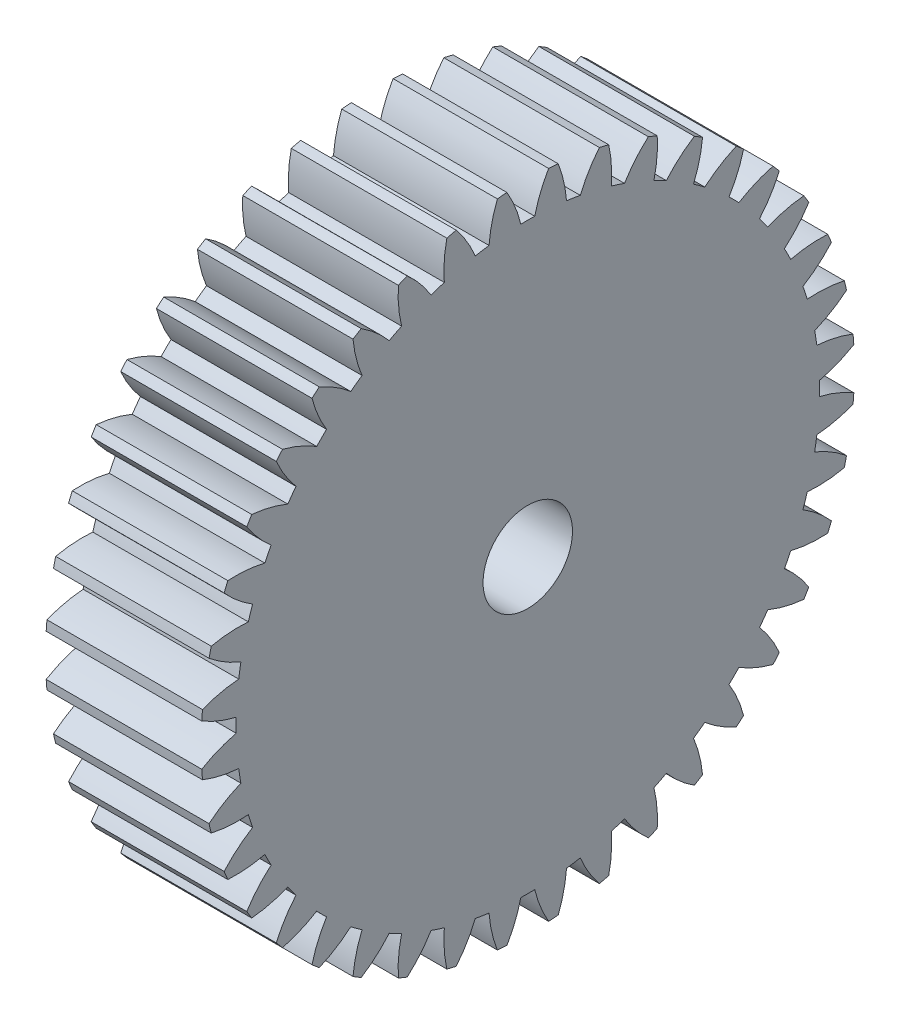
SolidWorks part; units mm, degrees
ref_plane "Front Plane" through (0, 0, 0) normal (0, 0, 1) x (1, 0, 0)
ref_plane "Top Plane" through (0, 0, 0) normal (0, 1, 0) x (1, 0, 0)
ref_plane "Right Plane" through (0, 0, 0) normal (1, 0, 0) x (0, 0, -1)
ref_plane "Plane1" through (-1.595, 0, 0) normal (1, 0, 0) x (0, 0, -1)
sketch "Sketch1" plane through (-1.595, 0, 0) normal (1, 0, 0) x (0, 0, -1)
  circle A0 centre (-8.0381, 6.9342) radius 0.4
  arc A1 (-16.421, 7.4699) -> (-15.535, 7.1132) centre (-14.7963, 10.2268) ccw
  arc A2 (-15.535, 7.1132) -> (-15.535, 6.7552) centre (-8.0381, 6.9342) ccw
  arc A3 (-15.535, 6.7552) -> (-16.421, 6.3985) centre (-14.7963, 3.6417) ccw
  arc A4 (-16.421, 6.3985) -> (-16.4016, 6.152) centre (-8.0381, 6.9342) ccw
  arc A5 (-16.4016, 6.152) -> (-15.4707, 5.9382) centre (-15.2282, 9.129) ccw
  arc A6 (-15.4707, 5.9382) -> (-15.4147, 5.5847) centre (-8.0381, 6.9342) ccw
  arc A7 (-15.4147, 5.5847) -> (-16.234, 5.0937) centre (-14.198, 2.625) ccw
  arc A8 (-16.234, 5.0937) -> (-16.1763, 4.8533) centre (-8.0381, 6.9342) ccw
  arc A9 (-16.1763, 4.8533) -> (-15.2234, 4.7878) centre (-15.483, 7.9773) ccw
  arc A10 (-15.2234, 4.7878) -> (-15.1128, 4.4473) centre (-8.0381, 6.9342) ccw
  arc A11 (-15.1128, 4.4473) -> (-15.8452, 3.8343) centre (-13.4481, 1.7144) ccw
  arc A12 (-15.8452, 3.8343) -> (-15.7506, 3.6058) centre (-8.0381, 6.9342) ccw
  arc A13 (-15.7506, 3.6058) -> (-14.7992, 3.6902) centre (-15.5545, 6.7998) ccw
  arc A14 (-14.7992, 3.6902) -> (-14.6366, 3.3712) centre (-8.0381, 6.9342) ccw
  arc A15 (-14.6366, 3.3712) -> (-15.2641, 2.6511) centre (-12.5649, 0.9324) ccw
  arc A16 (-15.2641, 2.6511) -> (-15.1349, 2.4403) centre (-8.0381, 6.9342) ccw
  arc A17 (-15.1349, 2.4403) -> (-14.2084, 2.6725) centre (-15.4409, 5.6256) ccw
  arc A18 (-14.2084, 2.6725) -> (-13.998, 2.3829) centre (-8.0381, 6.9342) ccw
  arc A19 (-13.998, 2.3829) -> (-14.5052, 1.5735) centre (-11.5703, 0.2981) ccw
  arc A20 (-14.5052, 1.5735) -> (-14.3446, 1.3854) centre (-8.0381, 6.9342) ccw
  arc A21 (-14.3446, 1.3854) -> (-13.4658, 1.7597) centre (-15.1451, 4.4837) ccw
  arc A22 (-13.4658, 1.7597) -> (-13.2127, 1.5066) centre (-8.0381, 6.9342) ccw
  arc A23 (-13.2127, 1.5066) -> (-13.5869, 0.6278) centre (-10.4887, -0.1727) ccw
  arc A24 (-13.5869, 0.6278) -> (-13.3989, 0.4672) centre (-8.0381, 6.9342) ccw
  arc A25 (-13.3989, 0.4672) -> (-12.5895, 0.9743) centre (-14.6742, 3.4021) ccw
  arc A26 (-12.5895, 0.9743) -> (-12.2999, 0.7639) centre (-8.0381, 6.9342) ccw
  arc A27 (-12.2999, 0.7639) -> (-12.5321, -0.1626) centre (-9.3467, -0.4686) ccw
  arc A28 (-12.5321, -0.1626) -> (-12.3212, -0.2918) centre (-8.0381, 6.9342) ccw
  arc A29 (-12.3212, -0.2918) -> (-11.6011, 0.3357) centre (-14.04, 2.4075) ccw
  arc A30 (-11.6011, 0.3357) -> (-11.2822, 0.1732) centre (-8.0381, 6.9342) ccw
  arc A31 (-11.2822, 0.1732) -> (-11.3666, -0.7782) centre (-8.1726, -0.5821) ccw
  arc A32 (-11.3666, -0.7782) -> (-11.1381, -0.8728) centre (-8.0381, 6.9342) ccw
  arc A33 (-11.1381, -0.8728) -> (-10.525, -0.1404) centre (-13.2579, 1.5243) ccw
  arc A34 (-10.525, -0.1404) -> (-10.1846, -0.251) centre (-8.0381, 6.9342) ccw
  arc A35 (-10.1846, -0.251) -> (-10.1191, -1.2039) centre (-6.9951, -0.5106) ccw
  arc A36 (-10.1191, -1.2039) -> (-9.8786, -1.2617) centre (-8.0381, 6.9342) ccw
  arc A37 (-9.8786, -1.2617) -> (-9.3877, -0.4423) centre (-12.3474, 0.7744) ccw
  arc A38 (-9.3877, -0.4423) -> (-9.0341, -0.4984) centre (-8.0381, 6.9342) ccw
  arc A39 (-9.0341, -0.4984) -> (-8.8204, -1.4293) centre (-5.8433, -0.2558) ccw
  arc A40 (-8.8204, -1.4293) -> (-8.5739, -1.4487) centre (-8.0381, 6.9342) ccw
  arc A41 (-8.5739, -1.4487) -> (-8.2171, -0.5626) centre (-11.3307, 0.1761) ccw
  arc A42 (-8.2171, -0.5626) -> (-7.8591, -0.5626) centre (-8.0381, 6.9342) ccw
  arc A43 (-7.8591, -0.5626) -> (-7.5024, -1.4487) centre (-4.7456, 0.1761) ccw
  arc A44 (-7.5024, -1.4487) -> (-7.2559, -1.4293) centre (-8.0381, 6.9342) ccw
  arc A45 (-7.2559, -1.4293) -> (-7.0422, -0.4984) centre (-10.233, -0.2558) ccw
  arc A46 (-7.0422, -0.4984) -> (-6.6886, -0.4423) centre (-8.0381, 6.9342) ccw
  arc A47 (-6.6886, -0.4423) -> (-6.1976, -1.2617) centre (-3.7289, 0.7744) ccw
  arc A48 (-6.1976, -1.2617) -> (-5.9572, -1.2039) centre (-8.0381, 6.9342) ccw
  arc A49 (-5.9572, -1.2039) -> (-5.8917, -0.251) centre (-9.0812, -0.5106) ccw
  arc A50 (-5.8917, -0.251) -> (-5.5512, -0.1404) centre (-8.0381, 6.9342) ccw
  arc A51 (-5.5512, -0.1404) -> (-4.9382, -0.8728) centre (-2.8184, 1.5243) ccw
  arc A52 (-4.9382, -0.8728) -> (-4.7097, -0.7782) centre (-8.0381, 6.9342) ccw
  arc A53 (-4.7097, -0.7782) -> (-4.7941, 0.1732) centre (-7.9037, -0.5821) ccw
  arc A54 (-4.7941, 0.1732) -> (-4.4752, 0.3357) centre (-8.0381, 6.9342) ccw
  arc A55 (-4.4752, 0.3357) -> (-3.7551, -0.2918) centre (-2.0363, 2.4075) ccw
  arc A56 (-3.7551, -0.2918) -> (-3.5442, -0.1626) centre (-8.0381, 6.9342) ccw
  arc A57 (-3.5442, -0.1626) -> (-3.7764, 0.7639) centre (-6.7296, -0.4686) ccw
  arc A58 (-3.7764, 0.7639) -> (-3.4868, 0.9743) centre (-8.0381, 6.9342) ccw
  arc A59 (-3.4868, 0.9743) -> (-2.6774, 0.4672) centre (-1.4021, 3.4021) ccw
  arc A60 (-2.6774, 0.4672) -> (-2.4894, 0.6278) centre (-8.0381, 6.9342) ccw
  arc A61 (-2.4894, 0.6278) -> (-2.8636, 1.5066) centre (-5.5876, -0.1727) ccw
  arc A62 (-2.8636, 1.5066) -> (-2.6105, 1.7597) centre (-8.0381, 6.9342) ccw
  arc A63 (-2.6105, 1.7597) -> (-1.7317, 1.3854) centre (-0.9312, 4.4837) ccw
  arc A64 (-1.7317, 1.3854) -> (-1.5711, 1.5735) centre (-8.0381, 6.9342) ccw
  arc A65 (-1.5711, 1.5735) -> (-2.0783, 2.3829) centre (-4.506, 0.2981) ccw
  arc A66 (-2.0783, 2.3829) -> (-1.8678, 2.6725) centre (-8.0381, 6.9342) ccw
  arc A67 (-1.8678, 2.6725) -> (-0.9413, 2.4403) centre (-0.6354, 5.6256) ccw
  arc A68 (-0.9413, 2.4403) -> (-0.8121, 2.6511) centre (-8.0381, 6.9342) ccw
  arc A69 (-0.8121, 2.6511) -> (-1.4397, 3.3712) centre (-3.5114, 0.9324) ccw
  arc A70 (-1.4397, 3.3712) -> (-1.2771, 3.6902) centre (-8.0381, 6.9342) ccw
  arc A71 (-1.2771, 3.6902) -> (-0.3257, 3.6058) centre (-0.5218, 6.7998) ccw
  arc A72 (-0.3257, 3.6058) -> (-0.2311, 3.8343) centre (-8.0381, 6.9342) ccw
  arc A73 (-0.2311, 3.8343) -> (-0.9635, 4.4473) centre (-2.6282, 1.7144) ccw
  arc A74 (-0.9635, 4.4473) -> (-0.8529, 4.7878) centre (-8.0381, 6.9342) ccw
  arc A75 (-0.8529, 4.7878) -> (0.1, 4.8533) centre (-0.5933, 7.9773) ccw
  arc A76 (0.1, 4.8533) -> (0.1577, 5.0937) centre (-8.0381, 6.9342) ccw
  arc A77 (0.1577, 5.0937) -> (-0.6616, 5.5847) centre (-1.8783, 2.625) ccw
  arc A78 (-0.6616, 5.5847) -> (-0.6056, 5.9382) centre (-8.0381, 6.9342) ccw
  arc A79 (-0.6056, 5.9382) -> (0.3254, 6.152) centre (-0.8481, 9.129) ccw
  arc A80 (0.3254, 6.152) -> (0.3448, 6.3985) centre (-8.0381, 6.9342) ccw
  arc A81 (0.3448, 6.3985) -> (-0.5413, 6.7552) centre (-1.28, 3.6417) ccw
  arc A82 (-0.5413, 6.7552) -> (-0.5413, 7.1132) centre (-8.0381, 6.9342) ccw
  arc A83 (-0.5413, 7.1132) -> (0.3448, 7.4699) centre (-1.28, 10.2268) ccw
  arc A84 (0.3448, 7.4699) -> (0.3254, 7.7165) centre (-8.0381, 6.9342) ccw
  arc A85 (0.3254, 7.7165) -> (-0.6056, 7.9302) centre (-0.8481, 4.7394) ccw
  arc A86 (-0.6056, 7.9302) -> (-0.6616, 8.2838) centre (-8.0381, 6.9342) ccw
  arc A87 (-0.6616, 8.2838) -> (0.1577, 8.7747) centre (-1.8783, 11.2434) ccw
  arc A88 (0.1577, 8.7747) -> (0.1, 9.0152) centre (-8.0381, 6.9342) ccw
  arc A89 (0.1, 9.0152) -> (-0.8529, 9.0806) centre (-0.5933, 5.8912) ccw
  arc A90 (-0.8529, 9.0806) -> (-0.9635, 9.4211) centre (-8.0381, 6.9342) ccw
  arc A91 (-0.9635, 9.4211) -> (-0.2311, 10.0342) centre (-2.6282, 12.154) ccw
  arc A92 (-0.2311, 10.0342) -> (-0.3257, 10.2626) centre (-8.0381, 6.9342) ccw
  arc A93 (-0.3257, 10.2626) -> (-1.2771, 10.1782) centre (-0.5218, 7.0687) ccw
  arc A94 (-1.2771, 10.1782) -> (-1.4397, 10.4972) centre (-8.0381, 6.9342) ccw
  arc A95 (-1.4397, 10.4972) -> (-0.8121, 11.2173) centre (-3.5114, 12.936) ccw
  arc A96 (-0.8121, 11.2173) -> (-0.9413, 11.4281) centre (-8.0381, 6.9342) ccw
  arc A97 (-0.9413, 11.4281) -> (-1.8678, 11.1959) centre (-0.6354, 8.2428) ccw
  arc A98 (-1.8678, 11.1959) -> (-2.0783, 11.4856) centre (-8.0381, 6.9342) ccw
  arc A99 (-2.0783, 11.4856) -> (-1.5711, 12.295) centre (-4.506, 13.5703) ccw
  arc A100 (-1.5711, 12.295) -> (-1.7317, 12.483) centre (-8.0381, 6.9342) ccw
  arc A101 (-1.7317, 12.483) -> (-2.6105, 12.1087) centre (-0.9312, 9.3847) ccw
  arc A102 (-2.6105, 12.1087) -> (-2.8636, 12.3619) centre (-8.0381, 6.9342) ccw
  arc A103 (-2.8636, 12.3619) -> (-2.4894, 13.2406) centre (-5.5876, 14.0411) ccw
  arc A104 (-2.4894, 13.2406) -> (-2.6774, 13.4012) centre (-8.0381, 6.9342) ccw
  arc A105 (-2.6774, 13.4012) -> (-3.4868, 12.8941) centre (-1.4021, 10.4663) ccw
  arc A106 (-3.4868, 12.8941) -> (-3.7764, 13.1045) centre (-8.0381, 6.9342) ccw
  arc A107 (-3.7764, 13.1045) -> (-3.5442, 14.031) centre (-6.7296, 14.337) ccw
  arc A108 (-3.5442, 14.031) -> (-3.7551, 14.1602) centre (-8.0381, 6.9342) ccw
  arc A109 (-3.7551, 14.1602) -> (-4.4752, 13.5327) centre (-2.0363, 11.461) ccw
  arc A110 (-4.4752, 13.5327) -> (-4.7941, 13.6952) centre (-8.0381, 6.9342) ccw
  arc A111 (-4.7941, 13.6952) -> (-4.7097, 14.6466) centre (-7.9037, 14.4506) ccw
  arc A112 (-4.7097, 14.6466) -> (-4.9382, 14.7413) centre (-8.0381, 6.9342) ccw
  arc A113 (-4.9382, 14.7413) -> (-5.5512, 14.0088) centre (-2.8184, 12.3441) ccw
  arc A114 (-5.5512, 14.0088) -> (-5.8917, 14.1195) centre (-8.0381, 6.9342) ccw
  arc A115 (-5.8917, 14.1195) -> (-5.9572, 15.0724) centre (-9.0812, 14.379) ccw
  arc A116 (-5.9572, 15.0724) -> (-6.1976, 15.1301) centre (-8.0381, 6.9342) ccw
  arc A117 (-6.1976, 15.1301) -> (-6.6886, 14.3108) centre (-3.7289, 13.0941) ccw
  arc A118 (-6.6886, 14.3108) -> (-7.0422, 14.3668) centre (-8.0381, 6.9342) ccw
  arc A119 (-7.0422, 14.3668) -> (-7.2559, 15.2977) centre (-10.233, 14.1242) ccw
  arc A120 (-7.2559, 15.2977) -> (-7.5024, 15.3171) centre (-8.0381, 6.9342) ccw
  arc A121 (-7.5024, 15.3171) -> (-7.8591, 14.4311) centre (-4.7456, 13.6924) ccw
  arc A122 (-7.8591, 14.4311) -> (-8.2171, 14.4311) centre (-8.0381, 6.9342) ccw
  arc A123 (-8.2171, 14.4311) -> (-8.5739, 15.3171) centre (-11.3307, 13.6924) ccw
  arc A124 (-8.5739, 15.3171) -> (-8.8204, 15.2977) centre (-8.0381, 6.9342) ccw
  arc A125 (-8.8204, 15.2977) -> (-9.0341, 14.3668) centre (-5.8433, 14.1242) ccw
  arc A126 (-9.0341, 14.3668) -> (-9.3877, 14.3108) centre (-8.0381, 6.9342) ccw
  arc A127 (-9.3877, 14.3108) -> (-9.8786, 15.1301) centre (-12.3474, 13.0941) ccw
  arc A128 (-9.8786, 15.1301) -> (-10.1191, 15.0724) centre (-8.0381, 6.9342) ccw
  arc A129 (-10.1191, 15.0724) -> (-10.1846, 14.1195) centre (-6.9951, 14.379) ccw
  arc A130 (-10.1846, 14.1195) -> (-10.525, 14.0088) centre (-8.0381, 6.9342) ccw
  arc A131 (-10.525, 14.0088) -> (-11.1381, 14.7413) centre (-13.2579, 12.3441) ccw
  arc A132 (-11.1381, 14.7413) -> (-11.3666, 14.6466) centre (-8.0381, 6.9342) ccw
  arc A133 (-11.3666, 14.6466) -> (-11.2822, 13.6952) centre (-8.1726, 14.4506) ccw
  arc A134 (-11.2822, 13.6952) -> (-11.6011, 13.5327) centre (-8.0381, 6.9342) ccw
  arc A135 (-11.6011, 13.5327) -> (-12.3212, 14.1602) centre (-14.04, 11.461) ccw
  arc A136 (-12.3212, 14.1602) -> (-12.5321, 14.031) centre (-8.0381, 6.9342) ccw
  arc A137 (-12.5321, 14.031) -> (-12.2999, 13.1045) centre (-9.3467, 14.337) ccw
  arc A138 (-12.2999, 13.1045) -> (-12.5895, 12.8941) centre (-8.0381, 6.9342) ccw
  arc A139 (-12.5895, 12.8941) -> (-13.3989, 13.4012) centre (-14.6742, 10.4663) ccw
  arc A140 (-13.3989, 13.4012) -> (-13.5869, 13.2406) centre (-8.0381, 6.9342) ccw
  arc A141 (-13.5869, 13.2406) -> (-13.2127, 12.3619) centre (-10.4887, 14.0411) ccw
  arc A142 (-13.2127, 12.3619) -> (-13.4658, 12.1087) centre (-8.0381, 6.9342) ccw
  arc A143 (-13.4658, 12.1087) -> (-14.3446, 12.483) centre (-15.1451, 9.3847) ccw
  arc A144 (-14.3446, 12.483) -> (-14.5052, 12.295) centre (-8.0381, 6.9342) ccw
  arc A145 (-14.5052, 12.295) -> (-13.998, 11.4856) centre (-11.5703, 13.5703) ccw
  arc A146 (-13.998, 11.4856) -> (-14.2084, 11.1959) centre (-8.0381, 6.9342) ccw
  arc A147 (-14.2084, 11.1959) -> (-15.1349, 11.4281) centre (-15.4409, 8.2428) ccw
  arc A148 (-15.1349, 11.4281) -> (-15.2641, 11.2173) centre (-8.0381, 6.9342) ccw
  arc A149 (-15.2641, 11.2173) -> (-14.6366, 10.4972) centre (-12.5649, 12.936) ccw
  arc A150 (-14.6366, 10.4972) -> (-14.7992, 10.1782) centre (-8.0381, 6.9342) ccw
  arc A151 (-14.7992, 10.1782) -> (-15.7506, 10.2626) centre (-15.5545, 7.0687) ccw
  arc A152 (-15.7506, 10.2626) -> (-15.8452, 10.0342) centre (-8.0381, 6.9342) ccw
  arc A153 (-15.8452, 10.0342) -> (-15.1128, 9.4211) centre (-13.4481, 12.154) ccw
  arc A154 (-15.1128, 9.4211) -> (-15.2234, 9.0806) centre (-8.0381, 6.9342) ccw
  arc A155 (-15.2234, 9.0806) -> (-16.1763, 9.0152) centre (-15.483, 5.8912) ccw
  arc A156 (-16.1763, 9.0152) -> (-16.234, 8.7747) centre (-8.0381, 6.9342) ccw
  arc A157 (-16.234, 8.7747) -> (-15.4147, 8.2838) centre (-14.198, 11.2434) ccw
  arc A158 (-15.4147, 8.2838) -> (-15.4707, 7.9302) centre (-8.0381, 6.9342) ccw
  arc A159 (-15.4707, 7.9302) -> (-16.4016, 7.7165) centre (-15.2282, 4.7394) ccw
  arc A160 (-16.4016, 7.7165) -> (-16.421, 7.4699) centre (-8.0381, 6.9342) ccw
extrude "Boss-Extrude1" add sketch "Sketch1" against normal blind 4
sketch "Sketch2" plane through (-1.595, 0, 0) normal (1, 0, 0) x (0, 0, -1)
  circle A0 centre (-8.0381, 6.9342) radius 1.15
  dimension "D1" = 2.3
extrude "Cut-Extrude1" cut sketch "Sketch2" against normal through all
